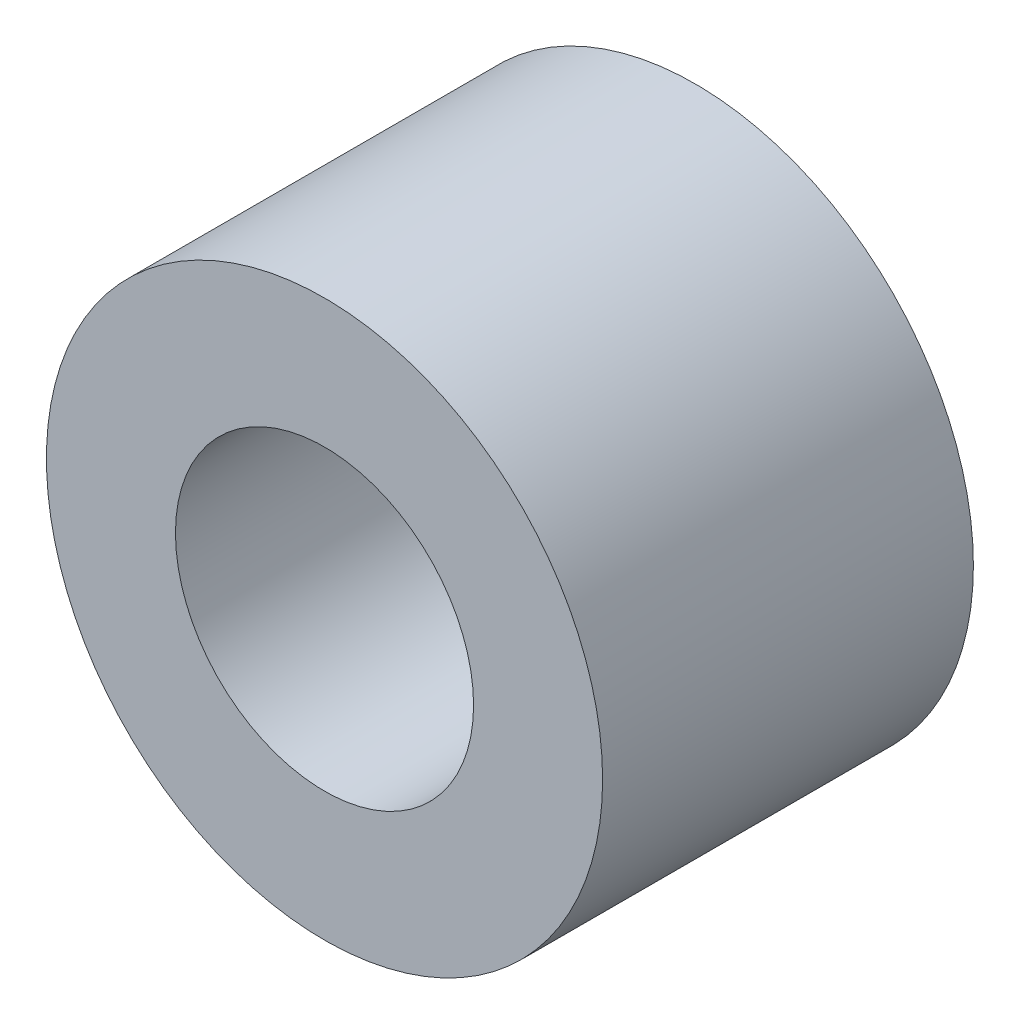
SolidWorks part; units mm, degrees
ref_plane "Front Plane" through (0, 0, 0) normal (0, 0, 1) x (1, 0, 0)
ref_plane "Top Plane" through (0, 0, 0) normal (0, 1, 0) x (1, 0, 0)
ref_plane "Right Plane" through (0, 0, 0) normal (1, 0, 0) x (0, 0, -1)
sketch "Sketch1" plane through (0, 0, 0) normal (0, 0, 1) x (1, 0, 0)
  circle A0 centre (0, 0) radius 2.5527
  circle A1 centre (0, 0) radius 4.7625
  dimension "D1" = 5.1054
  dimension "D2" = 9.525
extrude "Boss-Extrude1" add sketch "Sketch1" along normal mid plane 6.35
